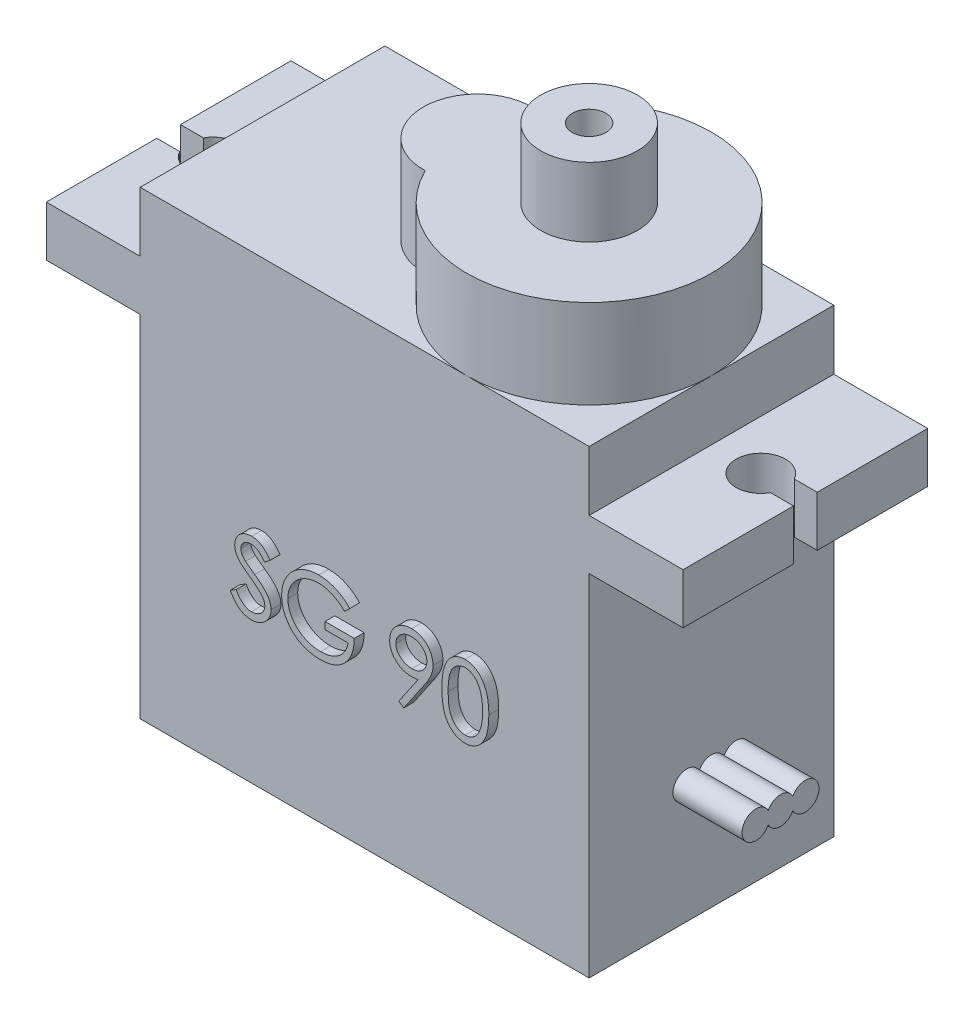
SolidWorks part; units mm, degrees
other "Markup1"
sketch "Sketch1" plane through (-16.135, 13.58, -6.2) normal (-0.0385, 0.6954, -0.7176) x (-0.9203, 0.2551, 0.2965)
other "Markup2"
sketch "Sketch2" plane through (-16.135, 13.58, -6.2) normal (-0.4026, 0.8193, -0.4082) x (0.8803, 0.4688, 0.0727)
other "Markup3"
sketch "Sketch3" plane through (-16.135, 13.58, -6.2) normal (-0.7443, 0.6276, -0.2285) x (0.6613, 0.7405, -0.1202)
ref_plane "Alzado" through (0, 0, 0) normal (0, 0, 1) x (1, 0, 0)
ref_plane "Planta" through (0, 0, 0) normal (0, 1, 0) x (1, 0, 0)
ref_plane "Vista lateral" through (0, 0, 0) normal (1, 0, 0) x (0, 0, -1)
sketch "Croquis1" plane through (0, 0, 0) normal (0, 0, 1) x (1, 0, 0)
  line L0 (-11.375, 0) -> (-16.135, 0)
  line L1 (-16.135, 0) -> (-16.135, 2.55)
  line L2 (-16.135, 2.55) -> (-11.375, 2.55)
  line L3 (-11.375, 2.55) -> (-11.375, 5.58)
  line L4 (-11.375, 5.58) -> (11.375, 5.58)
  line L5 (0, 0) -> (0, 5.58) construction
  line L6 (-11.375, 0) -> (-11.375, -17.75)
  line L7 (-11.375, -17.75) -> (11.375, -17.75)
  line L8 (0, -17.75) -> (0, 0) construction
  line L9 (11.375, 0) -> (11.375, -17.75)
  line L10 (11.375, 2.55) -> (11.375, 5.58)
  line L11 (16.135, 2.55) -> (11.375, 2.55)
  line L12 (16.135, 0) -> (16.135, 2.55)
  line L13 (11.375, 0) -> (16.135, 0)
  dimension "D1" = 11.375
  dimension "D2" = 16.135
  dimension "D3" = 17.75
  dimension "D4" = 2.55
  dimension "D5" = 23.33
extrude "Saliente-Extruir1" add sketch "Croquis1" along normal mid plane 12.4
sketch "Croquis2" plane through (0, 0, 0) normal (0, 1, 0) x (1, 0, 0)
  line L0 (-11.375, 0) -> (11.375, 0) construction
  line L1 (-11.375, -6.2) -> (-11.375, 6.2) construction
  line L2 (11.375, -6.2) -> (11.375, 6.2) construction
  line L3 (11.375, 6.2) -> (-11.375, 6.2) construction
  circle A0 centre (5.175, 0) radius 6.2
  circle A1 centre (-0.475, 0) radius 2.75
  point P8 (5.175, 6.2)
  point P9 (-3.225, 0)
  point P15 (11.375, 0)
  dimension "D1" = 5.5
  dimension "D2" = 14.6
extrude "Saliente-Extruir2" add sketch "Croquis2" along normal blind 4.5 from surface at 5.58 contours A1 L0 A0 | A0 L0 A1 | L0 A0 A1 | L0 A1 A0 | L0 A1 A0 | A1 L0 A0 starting at face at (0, 5.58, 0)
sketch "Croquis3" plane through (0, 0, 0) normal (0, 1, 0) x (1, 0, 0)
  circle A0 centre (5.175, 0) radius 2.45
  circle A1 centre (5.175, 0) radius 0.85
  dimension "D1" = 4.9
  dimension "D2" = 1.7
extrude "Saliente-Extruir3" add sketch "Croquis3" along normal blind 3.5 from surface contours A0
sketch "Croquis4" plane through (0, 0, 0) normal (1, 0, 0) x (0, 0, -1)
  line L0 (0, -17.75) -> (0, 0) construction
  line L1 (-6.2, -17.75) -> (6.2, -17.75) construction
  line L2 (-1.25, -11.75) -> (1.25, -11.75) construction
  circle A0 centre (0, -11.75) radius 0.7
  circle A1 centre (1.25, -11.75) radius 0.7
  circle A2 centre (-1.25, -11.75) radius 0.7
  dimension "D1" = 1.4
  dimension "D2" = 6
  dimension "D3" = 2.5
extrude "Saliente-Extruir5" add sketch "Croquis4" along normal blind 3.5 from vertex at 11.375 contours A0 A1 | A0 A1 | A0 A2 A1 | A2 A0 | A2 A0 starting at point (11.375, -17.75, -6.2)
sketch "Croquis5" plane through (0, 0, 0) normal (0, 1, 0) x (1, 0, 0)
  line L0 (-16.135, 0) -> (-11.375, 0) construction
  line L1 (-16.135, -6.2) -> (-16.135, 6.2) construction
  line L2 (-11.375, -6.2) -> (-11.375, 6.2) construction
  line L3 (-11.375, 0) -> (11.375, 0) construction
  line L4 (11.375, -6.2) -> (11.375, 6.2) construction
  line L5 (11.375, 0) -> (16.135, 0) construction
  line L6 (16.135, -6.2) -> (16.135, 6.2) construction
  line L8 (-17.6468, -0.6) -> (-14.6232, -0.6)
  line L9 (-17.6468, -0.6) -> (-17.6468, 0.6)
  line L10 (-17.6468, 0.6) -> (-14.6232, 0.6)
  line L11 (-14.6232, -0.6) -> (-14.6232, 0.6)
  line L12 (-17.6468, -0.6) -> (-14.6232, 0.6) construction
  line L13 (-17.6468, 0.6) -> (-14.6232, -0.6) construction
  circle A0 centre (-13.875, 0) radius 1.25
  dimension "D2" = 2.5
  dimension "D1" = 2.5
  dimension "D3" = 1.2
extrude "Cortar-Extruir1" cut sketch "Croquis5" along normal blind 3.5 contours L10 L11 L8 L9 | A0
mirror "Simetría1" about plane through (0, 0, 0) normal (1, 0, 0) of "Cortar-Extruir1"
sketch "Croquis6" plane through (0, 0, 0) normal (0, 1, 0) x (1, 0, 0)
  text T0 "LM"
extrude "Cortar-Extruir2" cut sketch "Croquis6" along normal blind 0.5 from vertex at -17.75 starting at point (-11.375, -17.75, -6.2)
sketch "Croquis7" plane through (0, 0, 0) normal (0, 0, 1) x (1, 0, 0)
  text T0 "SG 90"
extrude "Saliente-Extruir6" add sketch "Croquis7" along normal blind 0.5 from surface at 6.2 starting at face at (0.3981, -0.6585, 6.2)
